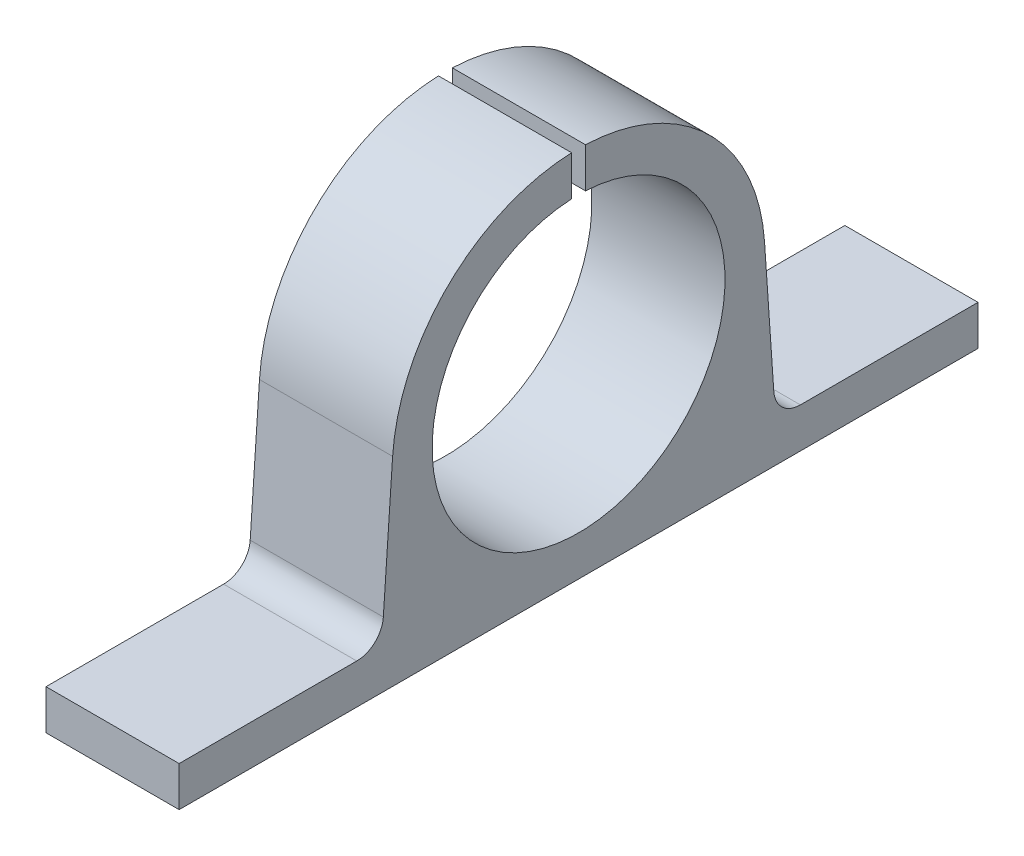
SolidWorks part; units mm, degrees
ref_plane "Front Plane" through (0, 0, 0) normal (0, 0, 1) x (1, 0, 0)
ref_plane "Top Plane" through (0, 0, 0) normal (0, 1, 0) x (1, 0, 0)
ref_plane "Right Plane" through (0, 0, 0) normal (1, 0, 0) x (0, 0, -1)
sketch "Sketch1" plane through (0, 0, 0) normal (1, 0, 0) x (0, 0, -1)
  line L0 (-15, 0) -> (15, 0)
  line L1 (-15, 0) -> (-9.5209, 17.0581)
  line L2 (9.5209, 17.0581) -> (15, 0)
  line L3 (0, 3) -> (-11, 3) construction
  line L4 (0, 25) -> (9.5209, 25) construction
  line L5 (0, 28) -> (15, 28) construction
  line L6 (-15, 0) -> (-13.5737, 20.6565) construction
  line L7 (0, 14) -> (0, 0) construction
  line L8 (15, 0) -> (13.5737, 20.6565) construction
  arc A0 (-9.5209, 17.0581) -> (9.5209, 17.0581) centre (0, 14) cw
  circle A1 centre (0, 14) radius 11 construction
  arc A2 (-12.5173, 7.7296) -> (13.1196, 9.1136) centre (0, 14) ccw construction
  arc A3 (13.9667, 14.9644) -> (-13.9667, 14.9644) centre (0, 14) ccw construction
  point P4 (0, 0)
  point P15 (7.5, 28)
  dimension "D2" = 10
  dimension "D4" = 22
  dimension "D1" = 30
  dimension "D3" = 14
  dimension "D5" = 3
extrude "Boss-Extrude1" add sketch "Sketch1" along normal blind 10
sketch "Sketch2" plane through (10, 0, 0) normal (1, 0, 0) x (0, 0, -1)
  circle A0 centre (0, 14) radius 11
  dimension "D1" = 22
sketch "Sketch4" plane through (10, 0, 0) normal (1, 0, 0) x (0, 0, -1)
  line L0 (15, 0) -> (13.5737, 20.6565) construction
  line L1 (-15, 0) -> (-13.5737, 20.6565) construction
  line L2 (15, 0) -> (13.5737, 20.6565)
  line L3 (-15, 0) -> (15, 0)
  line L4 (15, 0) -> (9.5209, 17.0581)
  line L5 (-9.5209, 17.0581) -> (-15, 0)
  line L6 (-15, 0) -> (15, 0)
  line L7 (15, 0) -> (9.5209, 17.0581)
  line L8 (-9.5209, 17.0581) -> (-15, 0)
  line L9 (-15, 0) -> (-13.5737, 20.6565)
  arc A0 (13.9667, 14.9644) -> (-13.9667, 14.9644) centre (0, 14) ccw construction
  arc A1 (9.5209, 17.0581) -> (-9.5209, 17.0581) centre (0, 14) ccw
  arc A2 (9.5209, 17.0581) -> (-9.5209, 17.0581) centre (0, 14) ccw
  arc A3 (13.9667, 14.9644) -> (-13.9667, 14.9644) centre (0, 14) ccw
  arc M6 (9.5209, 17.0581) -> (-9.5209, 17.0581) centre (0, 14) ccw
  line M7 (-9.5209, 17.0581) -> (-15, 0)
  line M9 (15, 0) -> (9.5209, 17.0581)
  dimension "D1" = 0
extrude "Boss-Extrude3" add sketch "Sketch4" against normal up to surface (10 mm away) contours L2 A3 L9 M7 M6 M9 up to face at (0, 10.2645, 0)
sketch "Sketch5" plane through (0, 0, 0) normal (0, -1, 0) x (1, 0, 0)
  line L0 (10, 15) -> (10, -15) construction
  line L1 (0, 30) -> (10, 30)
  line L2 (0, 30) -> (0, -30)
  line L3 (0, -30) -> (10, -30)
  line L4 (10, 30) -> (10, -30)
  line L5 (0, 15) -> (0, -15) construction
  point P9 (0, 0)
  dimension "D1" = 60
extrude "Boss-Extrude4" add sketch "Sketch5" against normal blind 3
fillet "Fillet2" radius 2 2 edges at (5, 3, -14.7929) (5, 3, 14.7929)
extrude "Enlèv. mat.-Extru.1" cut sketch "Sketch2" against normal through all
sketch "Esquisse3" plane through (10, 0, 0) normal (1, 0, 0) x (0, 0, -1)
  line L1 (0.5212, 29.1887) -> (-0.5212, 29.1887)
  line L2 (0.5212, 29.1887) -> (0.5212, 24.1258)
  line L3 (0.5212, 24.1258) -> (-0.5212, 24.1258)
  line L4 (-0.5212, 29.1887) -> (-0.5212, 24.1258)
  line L5 (0.5212, 29.1887) -> (-0.5212, 24.1258) construction
  line L6 (0.5212, 24.1258) -> (-0.5212, 29.1887) construction
  point P0 (0, 26.6573)
extrude "Enlèv. mat.-Extru.2" cut sketch "Esquisse3" against normal through all
